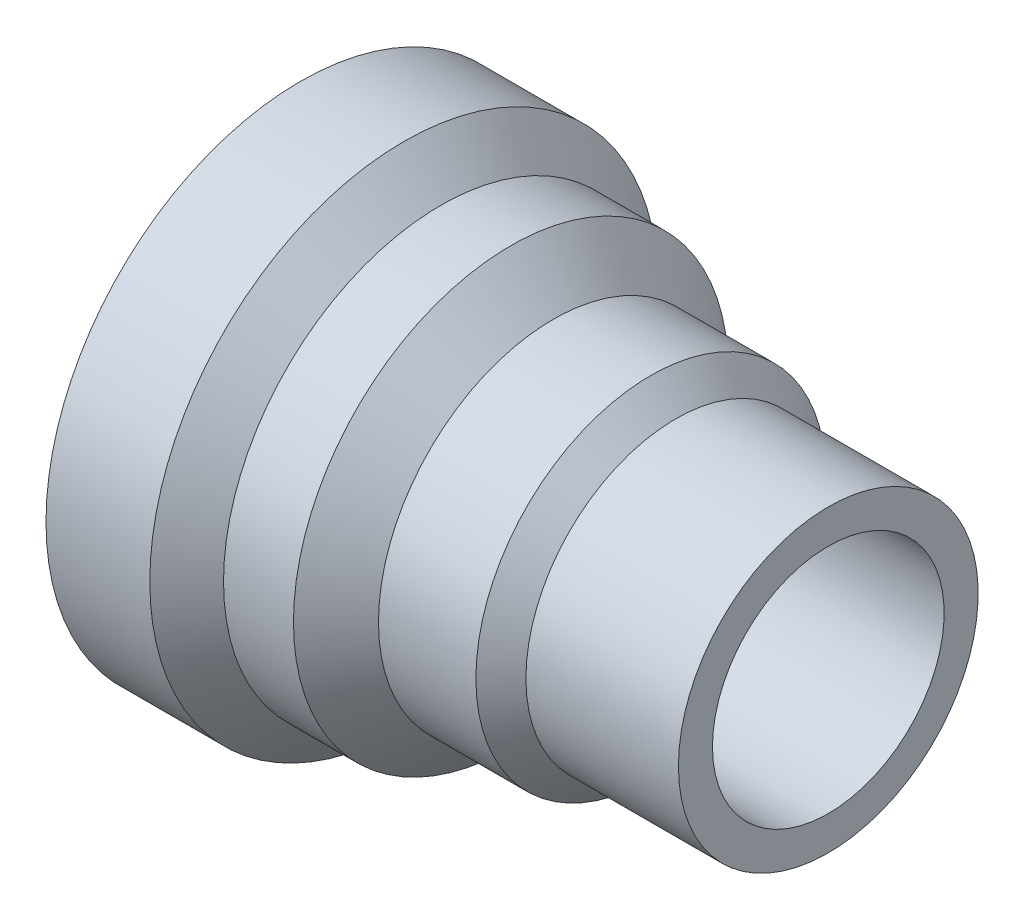
SolidWorks part; units mm, degrees
ref_plane "Front Plane" through (0, 0, 0) normal (0, 0, 1) x (1, 0, 0)
ref_plane "Top Plane" through (0, 0, 0) normal (0, 1, 0) x (1, 0, 0)
ref_plane "Right Plane" through (0, 0, 0) normal (1, 0, 0) x (0, 0, -1)
sketch "Sketch2" plane through (0, 0, 0) normal (0, 0, 1) x (1, 0, 0)
  line L0 (-34.6699, 16.2466) -> (29.6052, 16.2466) construction
  line L1 (-34.6699, 30.3469) -> (-34.6699, 47.1939)
  line L2 (-34.6699, 47.1939) -> (-22.0346, 47.1939)
  line L3 (-22.0346, 47.1939) -> (-17.5482, 42.7075)
  line L4 (-17.5482, 42.7075) -> (-9.0331, 42.7075)
  line L5 (-9.0331, 42.7075) -> (-3.86, 37.5344)
  line L6 (-3.86, 37.5344) -> (7.9971, 37.5344)
  line L7 (7.9971, 37.5344) -> (11.0414, 34.49)
  line L8 (11.0414, 34.49) -> (29.6052, 34.49)
  line L9 (29.6052, 34.49) -> (29.6052, 30.3469)
  line L10 (29.6052, 30.3469) -> (-34.6699, 30.3469)
revolve "Revolve2" add sketch "Sketch2" angle 360 about L0
